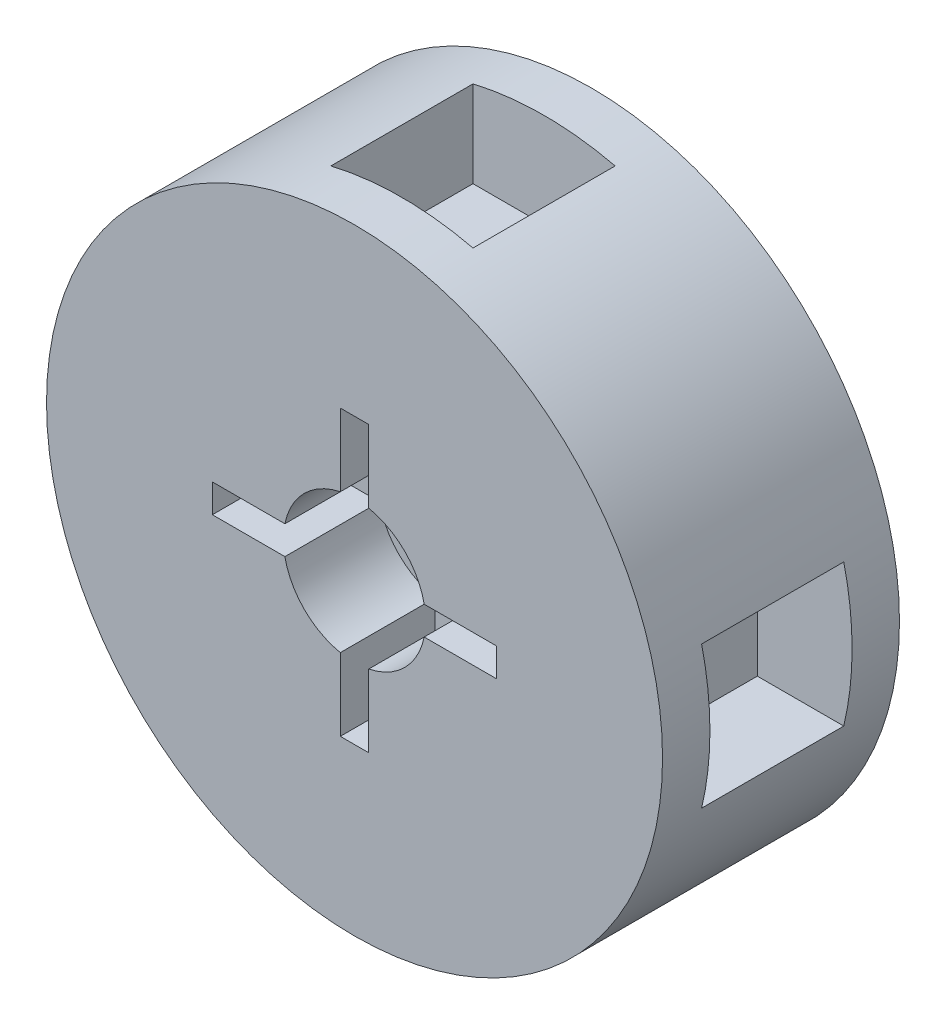
SolidWorks part; units mm, degrees
ref_plane "Front Plane" through (0, 0, 0) normal (0, 0, 1) x (1, 0, 0)
ref_plane "Top Plane" through (0, 0, 0) normal (0, 1, 0) x (1, 0, 0)
ref_plane "Right Plane" through (0, 0, 0) normal (1, 0, 0) x (0, 0, -1)
sketch "Sketch1" plane through (0, 0, 0) normal (0, 0, 1) x (1, 0, 0)
  circle A0 centre (0, 0) radius 32.5
  dimension "D1" = 65
extrude "Boss-Extrude1" add sketch "Sketch1" along normal blind 25
sketch "Sketch2" plane through (0, 0, 0) normal (0, 0, -1) x (-1, 0, 0)
  circle A0 centre (0, 0) radius 20
  dimension "D1" = 40
extrude "Cut-Extrude1" cut sketch "Sketch2" against normal blind 10
sketch "Sketch3" plane through (0, 0, 25) normal (0, 0, 1) x (1, 0, 0)
  line L0 (0, 0) -> (0, 15) construction
  line L1 (0, 15) -> (0, 0) construction
  line L2 (0, 0) -> (15, 0) construction
  line L3 (0, 0) -> (0, -15) construction
  line L4 (0, 0) -> (-15, 0) construction
  line L5 (15, -1.5) -> (15, 1.5)
  line L6 (-15, -1.5) -> (15, -1.5)
  line L7 (-15, -1.5) -> (-15, 1.5)
  line L8 (-15, 0) -> (15, 0)
  line L9 (0, -1.5) -> (0, 0)
  line L10 (-15, 1.5) -> (15, 1.5)
  line L11 (-1.5, -15) -> (1.5, -15)
  line L12 (1.5, 15) -> (1.5, -15)
  line L13 (-1.5, 15) -> (1.5, 15)
  line L14 (-1.5, 15) -> (-1.5, -15)
  line L15 (-15, 1.5) -> (-15, -1.5)
  line L16 (15, -1.5) -> (-15, -1.5)
  line L17 (15, 1.5) -> (15, -1.5)
  line L18 (15, 1.5) -> (-15, 1.5)
  line L19 (1.5, 15) -> (-1.5, 15)
  line L20 (-1.5, -15) -> (-1.5, 15)
  line L21 (1.5, -15) -> (-1.5, -15)
  line L22 (1.5, -15) -> (1.5, 15)
  circle A0 centre (0, 0) radius 7.5
  point P10 (0, 0)
  point P13 (0, 0)
  point P28 (0, 0)
  dimension "D1" = 15
  dimension "D2" = 15
  dimension "D4" = 1.5
  dimension "D6" = 15
  dimension "D7" = 1.5
  dimension "D3" = 4
  dimension "D5" = 4
extrude "Cut-Extrude2" cut sketch "Sketch3" against normal blind 10 contours L20 A0 L18 | A0 L10 L7 L8 | A0 L8 L7 L6 | L18 A0 L8 L14 | L8 A0 L16 L14 | L16 A0 L14 | L14 A0 L12 L6 | L12 A0 L6 | L6 A0 L8 L12 | L8 A0 L10 L12 | L10 A0 L22 | A0 L12 L13 L14 | L22 A0 L20 L10 | L10 L14 L8 L12 | L12 L8 L9 L6 | A0 L16 L5 L8 | A0 L8 L5 L18
ref_plane "Plane2" through (32.5, 0, 0) normal (1, 0, 0) x (0, 0, -1)
sketch "Sketch4" plane through (32.5, 0, 0) normal (1, 0, 0) x (0, 0, -1)
  line L0 (-25, 0) -> (0, 0) construction
  line L1 (-25, 32.5) -> (-25, -32.5) construction
  line L2 (0, 0) -> (0, -5) construction
  line L3 (0, -32.5) -> (0, 32.5) construction
  line L4 (0, -5) -> (-12.5, -5) construction
  line L5 (-12.5, -5) -> (-12.5, 0) construction
  line L7 (-5, -7.5) -> (-20, -7.5)
  line L8 (-5, -7.5) -> (-5, 7.5)
  line L9 (-5, 7.5) -> (-20, 7.5)
  line L10 (-20, -7.5) -> (-20, 7.5)
  line L11 (-5, -7.5) -> (-20, 7.5) construction
  line L12 (-5, 7.5) -> (-20, -7.5) construction
  dimension "D1" = 5
  dimension "D2" = 12.5
  dimension "D3" = 15
  dimension "D4" = 15
sketch "Sketch5" plane through (32.5, 0, 0) normal (1, 0, 0) x (0, 0, -1)
extrude "Cut-Extrude3" cut sketch "Sketch4" against normal blind 10
ref_plane "Plane4" through (-32.5, 0, 0) normal (-1, 0, 0) x (0, 0, 1)
sketch "Sketch6" plane through (-32.5, 0, 0) normal (-1, 0, 0) x (0, 0, 1)
  line L0 (0, 0) -> (25, 0) construction
  line L1 (25, -32.5) -> (25, 32.5) construction
  line L3 (20, -7.5) -> (5, -7.5)
  line L4 (20, -7.5) -> (20, 7.5)
  line L5 (20, 7.5) -> (5, 7.5)
  line L6 (5, -7.5) -> (5, 7.5)
  line L7 (20, -7.5) -> (5, 7.5) construction
  line L8 (20, 7.5) -> (5, -7.5) construction
  point P5 (12.5, 0)
  dimension "D1" = 15
  dimension "D2" = 15
extrude "Cut-Extrude4" cut sketch "Sketch6" against normal blind 10
ref_plane "Plane5" through (0, 32.5, 0) normal (0, 1, 0) x (1, 0, 0)
ref_plane "Plane6" through (0, -32.5, 0) normal (0, -1, 0) x (-1, 0, 0)
sketch "Sketch7" plane through (0, 32.5, 0) normal (0, 1, 0) x (1, 0, 0)
  line L0 (0, 0) -> (0, -25) construction
  line L2 (7.5, -20) -> (-7.5, -20)
  line L3 (7.5, -20) -> (7.5, -5)
  line L4 (7.5, -5) -> (-7.5, -5)
  line L5 (-7.5, -20) -> (-7.5, -5)
  line L6 (7.5, -20) -> (-7.5, -5) construction
  line L7 (7.5, -5) -> (-7.5, -20) construction
  point P3 (0, -12.5)
  dimension "D1" = 25
  dimension "D2" = 15
  dimension "D3" = 15
extrude "Cut-Extrude5" cut sketch "Sketch7" against normal blind 10
sketch "Sketch8" plane through (0, -32.5, 0) normal (0, -1, 0) x (-1, 0, 0)
  line L0 (0, 0) -> (0, -25) construction
  line L1 (-32.5, -25) -> (32.5, -25) construction
  line L3 (-7.5, -20) -> (7.5, -20)
  line L4 (-7.5, -20) -> (-7.5, -5)
  line L5 (-7.5, -5) -> (7.5, -5)
  line L6 (7.5, -20) -> (7.5, -5)
  line L7 (-7.5, -20) -> (7.5, -5) construction
  line L8 (-7.5, -5) -> (7.5, -20) construction
  point P5 (0, -12.5)
  dimension "D1" = 15
  dimension "D2" = 15
extrude "Cut-Extrude6" cut sketch "Sketch8" against normal blind 10
